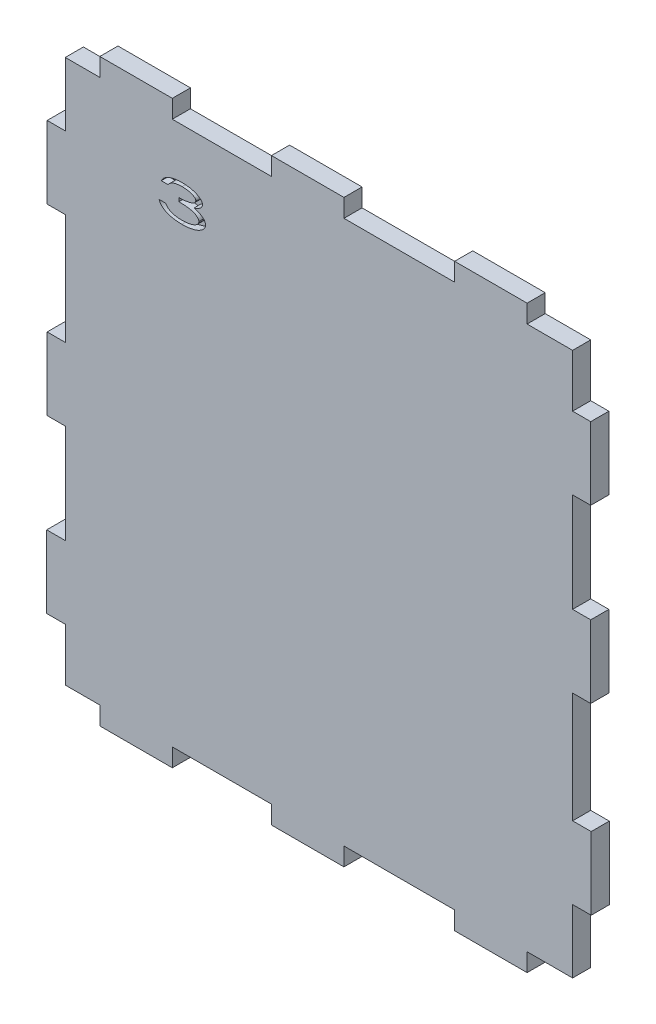
SolidWorks part; units mm, degrees
ref_plane "Front Plane" through (0, 0, 0) normal (0, 0, 1) x (1, 0, 0)
ref_plane "Top Plane" through (0, 0, 0) normal (0, 1, 0) x (1, 0, 0)
ref_plane "Right Plane" through (0, 0, 0) normal (1, 0, 0) x (0, 0, -1)
sketch "Sketch2" plane through (0, 0, 0) normal (0, 0, 1) x (1, 0, 0)
  line L1 (-70, -75) -> (-60.46, -75)
  line L2 (-70, -75) -> (-70, -60.46)
  line L3 (-70, 75) -> (-60.46, 75)
  line L4 (70, -75) -> (70, -57.44)
  line L5 (-70, -75) -> (70, 75) construction
  line L6 (-70, 75) -> (70, -75) construction
  line L7 (-60.46, 75) -> (-60.46, 80)
  line L8 (-40.46, 75) -> (-40.46, 80)
  line L9 (-60.46, 80) -> (-40.46, 80)
  line L10 (-40.46, 75) -> (-13.1, 75)
  line L12 (-13.1, 75) -> (-13.1, 80)
  line L13 (6.9, 75) -> (6.9, 80)
  line L14 (-13.1, 80) -> (6.9, 80)
  line L16 (37.44, 75) -> (37.44, 80)
  line L17 (57.44, 75) -> (57.44, 80)
  line L18 (37.44, 80) -> (57.44, 80)
  line L19 (6.9, 75) -> (37.44, 75)
  line L20 (57.44, 75) -> (70, 75)
  line L22 (-70, 57.44) -> (-75, 57.44)
  line L23 (-70, 37.44) -> (-75, 37.44)
  line L24 (-75, 57.44) -> (-75, 37.44)
  line L26 (-70, 6.9) -> (-75, 6.9)
  line L27 (-70, -13.1) -> (-75, -13.1)
  line L28 (-75, 6.9) -> (-75, -13.1)
  line L30 (-70, -40.46) -> (-75.1237, -40.46)
  line L31 (-70, -60.46) -> (-75.1237, -60.46)
  line L32 (-75.1237, -40.46) -> (-75.1237, -60.46)
  line L33 (-70, 57.44) -> (-70, 75)
  line L34 (-70, 6.9) -> (-70, 37.44)
  line L36 (0, 0) -> (18.0575, 0) construction
  line L37 (57.44, -75) -> (57.44, -80)
  line L38 (37.44, -80) -> (57.44, -80)
  line L39 (37.44, -75) -> (37.44, -80)
  line L40 (6.9, -75) -> (6.9, -80)
  line L41 (-13.1, -80) -> (6.9, -80)
  line L42 (-13.1, -75) -> (-13.1, -80)
  line L43 (-40.46, -75) -> (-40.46, -80)
  line L44 (-60.46, -80) -> (-40.46, -80)
  line L45 (-60.46, -75) -> (-60.46, -80)
  line L46 (70, -57.44) -> (75.1237, -57.44)
  line L47 (75.1237, -37.44) -> (75.1237, -57.44)
  line L48 (70, -37.44) -> (75.1237, -37.44)
  line L49 (70, -6.9) -> (75, -6.9)
  line L50 (75, 13.1) -> (75, -6.9)
  line L51 (70, 13.1) -> (75, 13.1)
  line L52 (70, 40.46) -> (75, 40.46)
  line L53 (75, 60.46) -> (75, 40.46)
  line L54 (70, 60.46) -> (75, 60.46)
  line L55 (-70, -40.46) -> (-70, -13.1)
  line L56 (-40.46, -75) -> (-13.1, -75)
  line L57 (6.9, -75) -> (37.44, -75)
  line L58 (57.44, -75) -> (70, -75)
  line L59 (70, -37.44) -> (70, -6.9)
  line L60 (70, 13.1) -> (70, 40.46)
  line L61 (70, 60.46) -> (70, 75)
  point P0 (0, 0)
  dimension "D1" = 150
  dimension "D2" = 140
  dimension "D3" = 9.54
  dimension "D4" = 20
  dimension "D5" = 27.36
  dimension "D6" = 20
  dimension "D7" = 5
  dimension "D8" = 5
  dimension "D9" = 5
  dimension "D10" = 30.54
  dimension "D11" = 20
  dimension "D12" = 5
  dimension "D13" = 17.56
  dimension "D14" = 20
  dimension "D15" = 5
  dimension "D16" = 30.54
  dimension "D17" = 20
  dimension "D18" = 5
  dimension "D19" = 27.36
  dimension "D20" = 20
  dimension "D21" = 14.54
  dimension "D22" = 20
  dimension "D23" = 27.36
  dimension "D24" = 20
  dimension "D25" = 30.54
  dimension "D26" = 20
extrude "Boss-Extrude1" add sketch "Sketch2" along normal blind 5
sketch "Sketch3" plane through (0, 0, 5) normal (0, 0, 1) x (1, 0, 0)
  text T0 "3\r\n" font "Century Gothic" height in points 36
extrude "Cut-Extrude1" cut sketch "Sketch3" against normal blind 2
